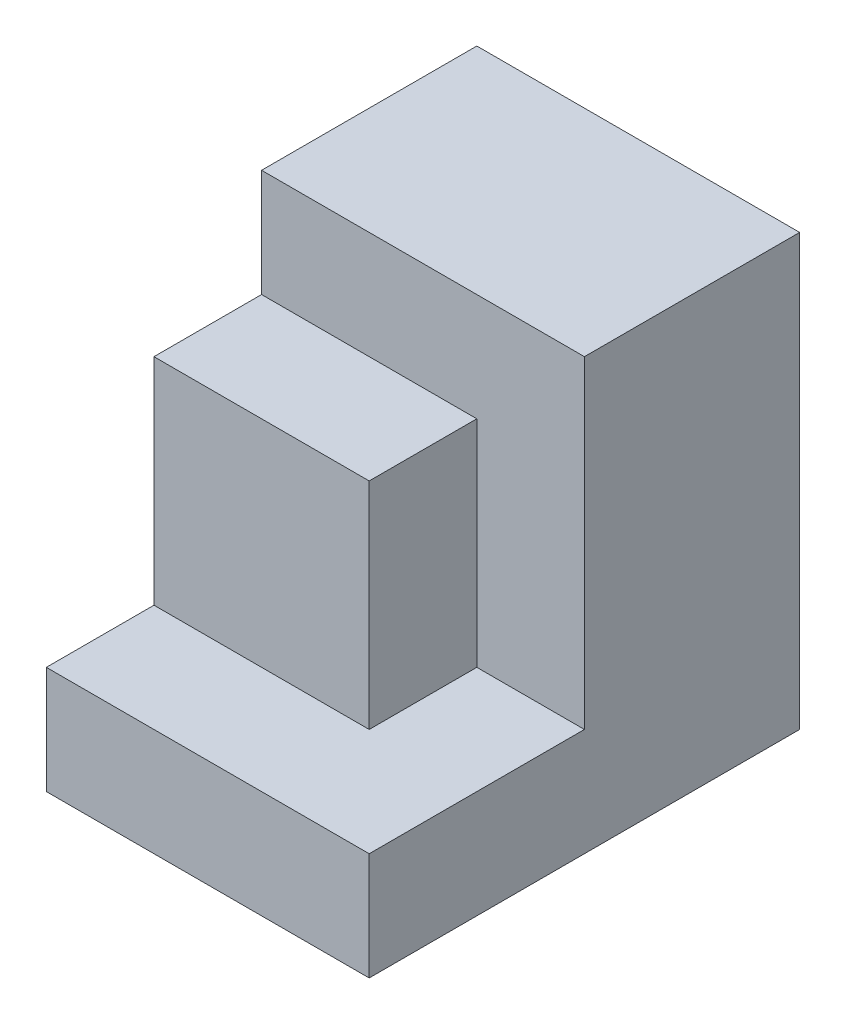
SolidWorks part; units mm, degrees
ref_plane "Front Plane" through (0, 0, 0) normal (0, 0, 1) x (1, 0, 0)
ref_plane "Top Plane" through (0, 0, 0) normal (0, 1, 0) x (1, 0, 0)
ref_plane "Right Plane" through (0, 0, 0) normal (1, 0, 0) x (0, 0, -1)
sketch "Sketch1" plane through (0, 0, 0) normal (0, 0, 1) x (1, 0, 0)
  line L1 (0, 0) -> (40, 0)
  line L2 (0, 0) -> (0, 40)
  line L3 (0, 40) -> (40, 40)
  line L4 (40, 0) -> (40, 40)
  dimension "D1" = 40
  dimension "D2" = 40
extrude "Boss-Extrude1" add sketch "Sketch1" along normal blind 40
sketch "Sketch2" plane through (0, 0, 40) normal (0, 0, 1) x (1, 0, 0)
  line L0 (10, 10) -> (0, 0)
  line L1 (0, 40) -> (10, 40)
  line L2 (0, 40) -> (0, 10)
  line L3 (0, 10) -> (10, 10)
  line L4 (10, 40) -> (10, 10)
  line L5 (0, 0) -> (0, 10)
  line M1 (0, 40) -> (0, 0)
  line M4 (40, 40) -> (0, 40)
  dimension "D1" = 10
  dimension "D2" = 30
extrude "Cut-Extrude1" cut sketch "Sketch2" against normal blind 40 contours L4 L3 M4 M1 | L3 L0 M1
sketch "Sketch3" plane through (0, 0, 0) normal (0, -1, 0) x (1, 0, 0)
  line L1 (0, 0) -> (10, 0)
  line L2 (0, 0) -> (0, 10)
  line L3 (0, 10) -> (10, 10)
  line L4 (10, 0) -> (10, 10)
  line L5 (0, 40) -> (10, 40)
  line L6 (0, 40) -> (0, 30)
  line L7 (0, 30) -> (10, 30)
  line L8 (10, 40) -> (10, 30)
  dimension "D1" = 10
  dimension "D2" = 10
  dimension "D3" = 10
  dimension "D4" = 10
extrude "Cut-Extrude2" cut sketch "Sketch3" against normal blind 40
sketch "Sketch4" plane through (0, 40, 0) normal (0, 1, 0) x (1, 0, 0)
  line L0 (40, -40) -> (40, 0) construction
  line L1 (10, -40) -> (40, -40)
  line L2 (10, -40) -> (10, -30)
  line L3 (10, -30) -> (40, -30)
  line L4 (40, -40) -> (40, -30)
  dimension "D1" = 10
extrude "Cut-Extrude3" cut sketch "Sketch4" against normal blind 30
sketch "Sketch5" plane through (0, 40, 0) normal (0, 1, 0) x (1, 0, 0)
  line L1 (40, -30) -> (30, -30)
  line L2 (40, -30) -> (40, -20)
  line L3 (40, -20) -> (30, -20)
  line L4 (30, -30) -> (30, -20)
  dimension "D1" = 10
  dimension "D2" = 10
extrude "Cut-Extrude4" cut sketch "Sketch5" against normal blind 30
sketch "Sketch6" plane through (0, 0, 30) normal (0, 0, 1) x (1, 0, 0)
  line L0 (30, 10) -> (30, 40) construction
  line L1 (10, 40) -> (30, 40)
  line L2 (10, 40) -> (10, 30)
  line L3 (10, 30) -> (30, 30)
  line L4 (30, 40) -> (30, 30)
  dimension "D1" = 10
extrude "Cut-Extrude6" cut sketch "Sketch6" against normal blind 10
